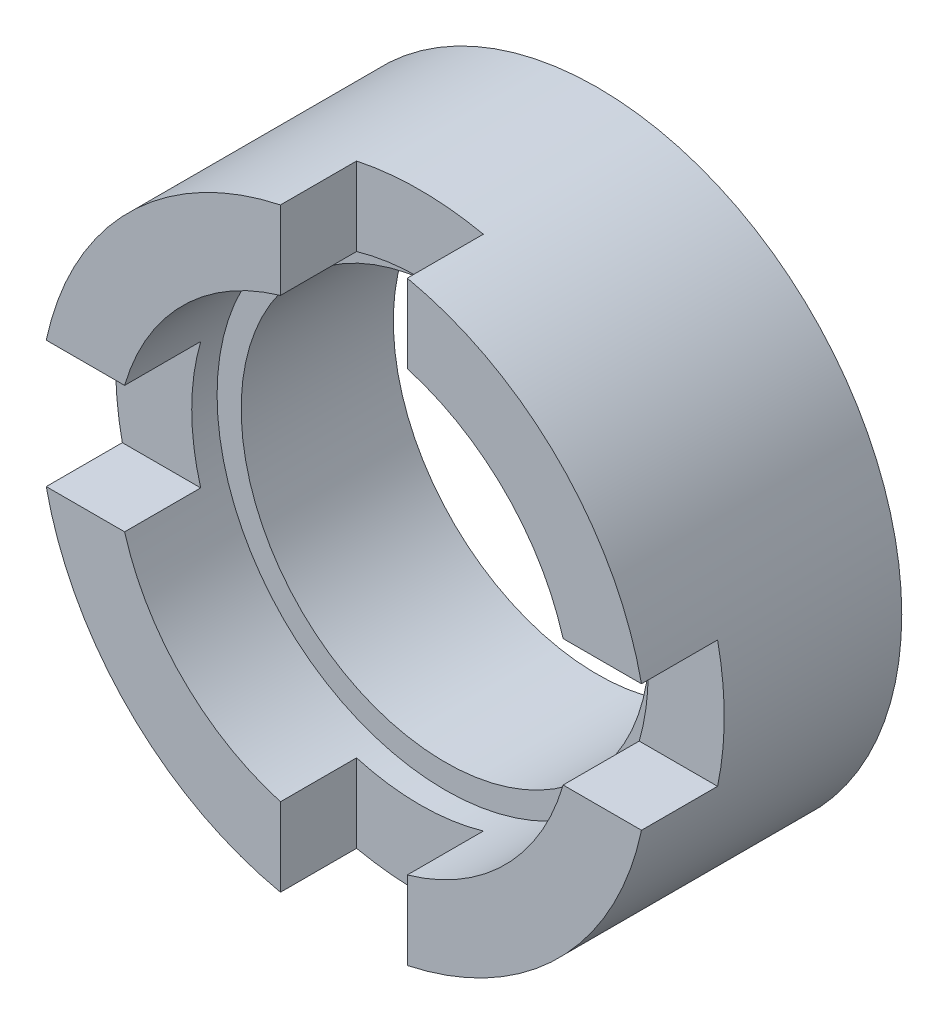
SolidWorks part; units mm, degrees
ref_plane "前视基准面" through (0, 0, 0) normal (0, 0, 1) x (1, 0, 0)
ref_plane "上视基准面" through (0, 0, 0) normal (0, 1, 0) x (1, 0, 0)
ref_plane "右视基准面" through (0, 0, 0) normal (1, 0, 0) x (0, 0, -1)
sketch "草图1" plane through (0, 0, 0) normal (0, 0, 1) x (1, 0, 0)
  circle A0 centre (0, 0) radius 8.05
  circle A1 centre (0, 0) radius 12
  dimension "D1" = 16.1
  dimension "D2" = 24
extrude "凸台-拉伸1" add sketch "草图1" along normal blind 10
sketch "草图3" plane through (0, 0, 10) normal (0, 0, 1) x (1, 0, 0)
  line L0 (-18.1676, 0) -> (19.0269, 0) construction
  line L1 (-16.5, 2.5) -> (-2.5, 2.5)
  line L2 (-16.5, 2.5) -> (-16.5, -2.5)
  line L3 (-16.5, -2.5) -> (-2.5, -2.5)
  line L4 (16.5, 2.5) -> (16.5, -2.5)
  line L5 (-2.5, 16.5) -> (2.5, 16.5)
  line L6 (-2.5, 16.5) -> (-2.5, 2.5)
  line L7 (-2.5, -16.5) -> (2.5, -16.5)
  line L8 (2.5, 16.5) -> (2.5, 2.5)
  line L9 (0, 13.161) -> (0, -13.4065) construction
  line L10 (2.5, 2.5) -> (16.5, 2.5)
  line L11 (-2.5, -2.5) -> (-2.5, -16.5)
  line L12 (2.5, -2.5) -> (16.5, -2.5)
  line L13 (2.5, -2.5) -> (2.5, -16.5)
  dimension "D1" = 5
  dimension "D2" = 14
  dimension "D3" = 14
extrude "切除-拉伸1" cut sketch "草图3" against normal blind 3
sketch "草图4" plane through (0, 0, 10) normal (0, 0, 1) x (1, 0, 0)
  circle A0 centre (0, 0) radius 9
  dimension "D1" = 18
extrude "切除-拉伸2" cut sketch "草图4" against normal blind 4
